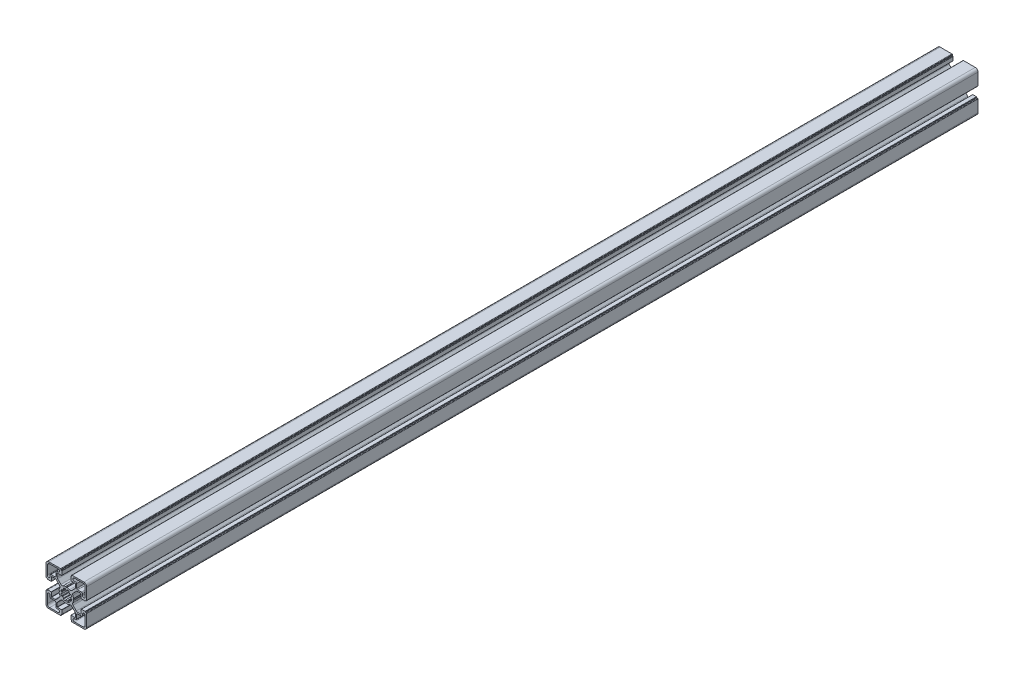
SolidWorks part; units mm, degrees
ref_plane "Front Plane" through (0, 0, 0) normal (0, 0, 1) x (1, 0, 0)
ref_plane "Top Plane" through (0, 0, 0) normal (0, 1, 0) x (1, 0, 0)
ref_plane "Right Plane" through (0, 0, 0) normal (1, 0, 0) x (0, 0, -1)
sketch "Sketch1" plane through (0, 0, 0) normal (0, 0, 1) x (1, 0, 0)
  line L0 (10.55, 18) -> (9, 18)
  line L1 (18.5, 21) -> (9, 21)
  line L2 (21, 9.0002) -> (21, 18.5)
  line L3 (18, 9.0002) -> (18, 10.55)
  line L4 (17, 11.55) -> (12.55, 11.55)
  line L5 (11.55, 12.55) -> (11.55, 17)
  line L6 (7.974, 0.7926) -> (7.5401, 0.0468)
  line L7 (-0.8674, 4.9242) -> (-0.9675, 5.4811)
  line L8 (-3.1913, 4.5626) -> (-2.864, 4.0985)
  line L9 (-4.0897, 2.8765) -> (-4.5668, 3.2082)
  line L10 (-5.4897, 0.9862) -> (-4.9205, 0.8878)
  line L11 (11.1298, 9.425) -> (7.5635, 5.8587)
  line L12 (16.3169, 9.9945) -> (12.5048, 9.9945)
  line L13 (16.5169, 5.2) -> (16.5169, 9.7945)
  line L14 (20.7196, 5) -> (16.7169, 5)
  line L15 (21.0196, 5.3) -> (21.0196, 5.5)
  line L16 (22, 5.8) -> (21.3196, 5.8)
  line L17 (22.5, 6.3) -> (22.5, 19.5)
  line L18 (19.5, 22.5) -> (6.3757, 22.5)
  line L19 (5.8757, 21.3) -> (5.8757, 22)
  line L20 (5.5757, 21) -> (5.3, 21)
  line L21 (5, 16.6668) -> (5, 20.7)
  line L22 (9.9054, 16.4668) -> (5.2, 16.4668)
  line L23 (10.1054, 12.4716) -> (10.1054, 16.2668)
  line L24 (5.9449, 7.4827) -> (9.5196, 11.0574)
  line L25 (0.1126, 7.6069) -> (0.7547, 7.9748)
  line L26 (5.4897, 0.9862) -> (4.9205, 0.8878)
  line L27 (4.0897, 2.8765) -> (4.5668, 3.2082)
  line L28 (3.1913, 4.5626) -> (2.864, 4.0985)
  line L29 (0.8674, 4.9242) -> (0.9675, 5.4811)
  line L30 (-10.55, -18) -> (-9, -18)
  line L31 (-18.5, -21) -> (-9, -21)
  line L32 (-21, -9.0002) -> (-21, -18.5)
  line L33 (-18, -9.0002) -> (-18, -10.55)
  line L34 (-17, -11.55) -> (-12.55, -11.55)
  line L35 (-11.55, -12.55) -> (-11.55, -17)
  line L36 (-7.974, -0.7926) -> (-7.5401, -0.0468)
  line L37 (-11.1298, -9.425) -> (-7.5635, -5.8587)
  line L38 (-16.3169, -9.9945) -> (-12.5048, -9.9945)
  line L39 (-16.5169, -5.2) -> (-16.5169, -9.7945)
  line L40 (-20.7196, -5) -> (-16.7169, -5)
  line L41 (-21.0196, -5.3) -> (-21.0196, -5.5)
  line L42 (-22, -5.8) -> (-21.3196, -5.8)
  line L43 (-22.5, -6.3) -> (-22.5, -19.5)
  line L44 (-19.5, -22.5) -> (-6.3757, -22.5)
  line L45 (-5.8757, -21.3) -> (-5.8757, -22)
  line L46 (-5.5757, -21) -> (-5.3, -21)
  line L47 (-5, -16.6668) -> (-5, -20.7)
  line L48 (-9.9054, -16.4668) -> (-5.2, -16.4668)
  line L49 (-10.1054, -12.4716) -> (-10.1054, -16.2668)
  line L50 (-5.9449, -7.4827) -> (-9.5196, -11.0574)
  line L51 (-0.1126, -7.6069) -> (-0.7547, -7.9748)
  line L52 (0.8674, -4.9242) -> (0.9675, -5.4811)
  line L53 (3.1913, -4.5626) -> (2.864, -4.0985)
  line L54 (4.0897, -2.8765) -> (4.5668, -3.2082)
  line L55 (5.4897, -0.9862) -> (4.9205, -0.8878)
  line L56 (0.1126, -7.6069) -> (0.7547, -7.9748)
  line L57 (5.9449, -7.4827) -> (9.5196, -11.0574)
  line L58 (10.1054, -12.4716) -> (10.1054, -16.2668)
  line L59 (9.9054, -16.4668) -> (5.2, -16.4668)
  line L60 (5, -16.6668) -> (5, -20.7)
  line L61 (5.5757, -21) -> (5.3, -21)
  line L62 (-0.1126, 7.6069) -> (-0.7547, 7.9748)
  line L63 (-5.9449, 7.4827) -> (-9.5196, 11.0574)
  line L64 (-10.1054, 12.4716) -> (-10.1054, 16.2668)
  line L65 (-9.9054, 16.4668) -> (-5.2, 16.4668)
  line L66 (-5, 16.6668) -> (-5, 20.7)
  line L67 (-5.5757, 21) -> (-5.3, 21)
  line L68 (-5.8757, 21.3) -> (-5.8757, 22)
  line L69 (-19.5, 22.5) -> (-6.3757, 22.5)
  line L70 (-22.5, 6.3) -> (-22.5, 19.5)
  line L71 (-22, 5.8) -> (-21.3196, 5.8)
  line L72 (-21.0196, 5.3) -> (-21.0196, 5.5)
  line L73 (-20.7196, 5) -> (-16.7169, 5)
  line L74 (-16.5169, 5.2) -> (-16.5169, 9.7945)
  line L75 (-16.3169, 9.9945) -> (-12.5048, 9.9945)
  line L76 (-11.1298, 9.425) -> (-7.5635, 5.8587)
  line L77 (-7.974, 0.7926) -> (-7.5401, 0.0468)
  line L78 (5.8757, -21.3) -> (5.8757, -22)
  line L79 (19.5, -22.5) -> (6.3757, -22.5)
  line L80 (22.5, -6.3) -> (22.5, -19.5)
  line L81 (22, -5.8) -> (21.3196, -5.8)
  line L82 (21.0196, -5.3) -> (21.0196, -5.5)
  line L83 (20.7196, -5) -> (16.7169, -5)
  line L84 (16.5169, -5.2) -> (16.5169, -9.7945)
  line L85 (16.3169, -9.9945) -> (12.5048, -9.9945)
  line L86 (11.1298, -9.425) -> (7.5635, -5.8587)
  line L87 (-5.4897, -0.9862) -> (-4.9205, -0.8878)
  line L88 (-4.0897, -2.8765) -> (-4.5668, -3.2082)
  line L89 (-3.1913, -4.5626) -> (-2.864, -4.0985)
  line L90 (-0.8674, -4.9242) -> (-0.9675, -5.4811)
  line L91 (7.974, -0.7926) -> (7.5401, -0.0468)
  line L92 (-11.55, 12.55) -> (-11.55, 17)
  line L93 (-17, 11.55) -> (-12.55, 11.55)
  line L94 (-18, 9.0002) -> (-18, 10.55)
  line L95 (-21, 9.0002) -> (-21, 18.5)
  line L96 (-18.5, 21) -> (-9, 21)
  line L97 (-10.55, 18) -> (-9, 18)
  line L98 (11.55, -12.55) -> (11.55, -17)
  line L99 (17, -11.55) -> (12.55, -11.55)
  line L100 (18, -9.0002) -> (18, -10.55)
  line L101 (21, -9.0002) -> (21, -18.5)
  line L102 (18.5, -21) -> (9, -21)
  line L103 (10.55, -18) -> (9, -18)
  line L104 (-33.3633, 0) -> (37.7265, 0) construction
  line L105 (0, 32.2957) -> (0, -36.0465) construction
  arc A0 (9, 18) -> (9, 21) centre (9, 19.5) cw
  arc A1 (18.5, 21) -> (21, 18.5) centre (18.5, 18.5) cw
  arc A2 (21, 9.0002) -> (18, 9.0002) centre (19.5, 9.0002) cw
  arc A3 (17, 11.55) -> (18, 10.55) centre (17, 10.55) cw
  arc A4 (12.55, 11.55) -> (11.55, 12.55) centre (12.55, 12.55) cw
  arc A5 (10.55, 18) -> (11.55, 17) centre (10.55, 17) cw
  arc A6 (7.5313, 0) -> (7.5401, 0.0468) centre (7.7309, -0.013) cw
  arc A7 (8, 0.9141) -> (7.974, 0.7926) centre (7.8011, 0.8932) cw
  arc A8 (7.2004, 3.6119) -> (8, 0.9141) centre (0.0496, 0.0249) cw
  arc A9 (7.2004, 3.6119) -> (7.5635, 5.8587) centre (8.9385, 4.4837) cw
  arc A10 (11.1298, 9.425) -> (12.5048, 9.9945) centre (12.5048, 8.05) cw
  arc A11 (16.3169, 9.9945) -> (16.5169, 9.7945) centre (16.3169, 9.7945) cw
  arc A12 (16.7169, 5) -> (16.5169, 5.2) centre (16.7169, 5.2) cw
  arc A13 (21.0196, 5.3) -> (20.7196, 5) centre (20.7196, 5.3) cw
  arc A14 (0.8674, 4.9242) -> (-0.8674, 4.9242) centre (0, 0) ccw
  arc A15 (-0.9675, 5.4811) -> (-1.5951, 5.8941) centre (-1.4627, 5.4119) ccw
  arc A16 (-1.5951, 5.8941) -> (-3.0444, 5.2994) centre (-0.0235, 0) ccw
  arc A17 (-3.0444, 5.2994) -> (-3.1913, 4.5626) centre (-2.7943, 4.8665) ccw
  arc A18 (-2.864, 4.0985) -> (-4.0897, 2.8765) centre (0, 0) ccw
  arc A19 (-4.5668, 3.2082) -> (-5.3025, 3.0565) centre (-4.868, 2.8091) ccw
  arc A20 (-5.3025, 3.0565) -> (-5.9068, 1.6112) centre (-0.0235, 0) ccw
  arc A21 (-5.9068, 1.6112) -> (-5.4897, 0.9862) centre (-5.4239, 1.4819) ccw
  arc A22 (-4.9205, 0.8878) -> (-5, 0) centre (0, 0) ccw
  arc A23 (21.0196, 5.5) -> (21.3196, 5.8) centre (21.3196, 5.5) cw
  arc A24 (22.5, 6.3) -> (22, 5.8) centre (22, 6.3) cw
  arc A25 (19.5, 22.5) -> (22.5, 19.5) centre (19.5, 19.5) cw
  arc A26 (5.8757, 22) -> (6.3757, 22.5) centre (6.3757, 22) cw
  arc A27 (5.8757, 21.3) -> (5.5757, 21) centre (5.5757, 21.3) cw
  arc A28 (5, 20.7) -> (5.3, 21) centre (5.3, 20.7) cw
  arc A29 (5.2, 16.4668) -> (5, 16.6668) centre (5.2, 16.6668) cw
  arc A30 (9.9054, 16.4668) -> (10.1054, 16.2668) centre (9.9054, 16.2668) cw
  arc A31 (10.1054, 12.4716) -> (9.5196, 11.0574) centre (8.1054, 12.4716) cw
  arc A32 (5.9449, 7.4827) -> (3.6665, 7.1733) centre (4.5855, 8.9496) cw
  arc A33 (0.8764, 8) -> (3.6665, 7.1733) centre (0.0235, 0) cw
  arc A34 (0.7547, 7.9748) -> (0.8764, 8) centre (0.8542, 7.8013) cw
  arc A35 (0.1126, 7.6069) -> (0, 7.531) centre (-0.0489, 7.7249) cw
  arc A36 (4.9205, 0.8878) -> (5, 0) centre (0, 0) cw
  arc A37 (5.9068, 1.6112) -> (5.4897, 0.9862) centre (5.4239, 1.4819) cw
  arc A38 (5.3025, 3.0565) -> (5.9068, 1.6112) centre (0.0235, 0) cw
  arc A39 (4.5668, 3.2082) -> (5.3025, 3.0565) centre (4.868, 2.8091) cw
  arc A40 (2.864, 4.0985) -> (4.0897, 2.8765) centre (0, 0) cw
  arc A41 (3.0444, 5.2994) -> (3.1913, 4.5626) centre (2.7943, 4.8665) cw
  arc A42 (1.5951, 5.8941) -> (3.0444, 5.2994) centre (0.0235, 0) cw
  arc A43 (0.9675, 5.4811) -> (1.5951, 5.8941) centre (1.4627, 5.4119) cw
  arc A44 (-9, -18) -> (-9, -21) centre (-9, -19.5) cw
  arc A45 (-18.5, -21) -> (-21, -18.5) centre (-18.5, -18.5) cw
  arc A46 (-21, -9.0002) -> (-18, -9.0002) centre (-19.5, -9.0002) cw
  arc A47 (-17, -11.55) -> (-18, -10.55) centre (-17, -10.55) cw
  arc A48 (-12.55, -11.55) -> (-11.55, -12.55) centre (-12.55, -12.55) cw
  arc A49 (-10.55, -18) -> (-11.55, -17) centre (-10.55, -17) cw
  arc A50 (-7.5313, 0) -> (-7.5401, -0.0468) centre (-7.7309, 0.013) cw
  arc A51 (-8, -0.9141) -> (-7.974, -0.7926) centre (-7.8011, -0.8932) cw
  arc A52 (-7.2004, -3.6119) -> (-8, -0.9141) centre (-0.0496, -0.0249) cw
  arc A53 (-7.2004, -3.6119) -> (-7.5635, -5.8587) centre (-8.9385, -4.4837) cw
  arc A54 (-11.1298, -9.425) -> (-12.5048, -9.9945) centre (-12.5048, -8.05) cw
  arc A55 (-16.3169, -9.9945) -> (-16.5169, -9.7945) centre (-16.3169, -9.7945) cw
  arc A56 (-16.7169, -5) -> (-16.5169, -5.2) centre (-16.7169, -5.2) cw
  arc A57 (-21.0196, -5.3) -> (-20.7196, -5) centre (-20.7196, -5.3) cw
  arc A58 (-21.0196, -5.5) -> (-21.3196, -5.8) centre (-21.3196, -5.5) cw
  arc A59 (-22.5, -6.3) -> (-22, -5.8) centre (-22, -6.3) cw
  arc A60 (-19.5, -22.5) -> (-22.5, -19.5) centre (-19.5, -19.5) cw
  arc A61 (-5.8757, -22) -> (-6.3757, -22.5) centre (-6.3757, -22) cw
  arc A62 (-5.8757, -21.3) -> (-5.5757, -21) centre (-5.5757, -21.3) cw
  arc A63 (-5, -20.7) -> (-5.3, -21) centre (-5.3, -20.7) cw
  arc A64 (-5.2, -16.4668) -> (-5, -16.6668) centre (-5.2, -16.6668) cw
  arc A65 (-9.9054, -16.4668) -> (-10.1054, -16.2668) centre (-9.9054, -16.2668) cw
  arc A66 (-10.1054, -12.4716) -> (-9.5196, -11.0574) centre (-8.1054, -12.4716) cw
  arc A67 (-5.9449, -7.4827) -> (-3.6665, -7.1733) centre (-4.5855, -8.9496) cw
  arc A68 (-0.8764, -8) -> (-3.6665, -7.1733) centre (-0.0235, 0) cw
  arc A69 (-0.7547, -7.9748) -> (-0.8764, -8) centre (-0.8542, -7.8013) cw
  arc A70 (-0.1126, -7.6069) -> (0, -7.531) centre (0.0489, -7.7249) cw
  arc A71 (0.9675, -5.4811) -> (1.5951, -5.8941) centre (1.4627, -5.4119) ccw
  arc A72 (1.5951, -5.8941) -> (3.0444, -5.2994) centre (0.0235, 0) ccw
  arc A73 (3.0444, -5.2994) -> (3.1913, -4.5626) centre (2.7943, -4.8665) ccw
  arc A74 (2.864, -4.0985) -> (4.0897, -2.8765) centre (0, 0) ccw
  arc A75 (4.5668, -3.2082) -> (5.3025, -3.0565) centre (4.868, -2.8091) ccw
  arc A76 (5.3025, -3.0565) -> (5.9068, -1.6112) centre (0.0235, 0) ccw
  arc A77 (5.9068, -1.6112) -> (5.4897, -0.9862) centre (5.4239, -1.4819) ccw
  arc A78 (4.9205, -0.8878) -> (5, 0) centre (0, 0) ccw
  arc A79 (0.1126, -7.6069) -> (0, -7.531) centre (-0.0489, -7.7249) ccw
  arc A80 (0.7547, -7.9748) -> (0.8764, -8) centre (0.8542, -7.8013) ccw
  arc A81 (0.8764, -8) -> (3.6665, -7.1733) centre (0.0235, 0) ccw
  arc A82 (5.9449, -7.4827) -> (3.6665, -7.1733) centre (4.5855, -8.9496) ccw
  arc A83 (10.1054, -12.4716) -> (9.5196, -11.0574) centre (8.1054, -12.4716) ccw
  arc A84 (9.9054, -16.4668) -> (10.1054, -16.2668) centre (9.9054, -16.2668) ccw
  arc A85 (5.2, -16.4668) -> (5, -16.6668) centre (5.2, -16.6668) ccw
  arc A86 (5, -20.7) -> (5.3, -21) centre (5.3, -20.7) ccw
  arc A87 (5.8757, -21.3) -> (5.5757, -21) centre (5.5757, -21.3) ccw
  arc A88 (-0.1126, 7.6069) -> (0, 7.531) centre (0.0489, 7.7249) ccw
  arc A89 (-0.7547, 7.9748) -> (-0.8764, 8) centre (-0.8542, 7.8013) ccw
  arc A90 (-0.8764, 8) -> (-3.6665, 7.1733) centre (-0.0235, 0) ccw
  arc A91 (-5.9449, 7.4827) -> (-3.6665, 7.1733) centre (-4.5855, 8.9496) ccw
  arc A92 (-10.1054, 12.4716) -> (-9.5196, 11.0574) centre (-8.1054, 12.4716) ccw
  arc A93 (-9.9054, 16.4668) -> (-10.1054, 16.2668) centre (-9.9054, 16.2668) ccw
  arc A94 (-5.2, 16.4668) -> (-5, 16.6668) centre (-5.2, 16.6668) ccw
  arc A95 (-5, 20.7) -> (-5.3, 21) centre (-5.3, 20.7) ccw
  arc A96 (-5.8757, 21.3) -> (-5.5757, 21) centre (-5.5757, 21.3) ccw
  arc A97 (-5.8757, 22) -> (-6.3757, 22.5) centre (-6.3757, 22) ccw
  arc A98 (-19.5, 22.5) -> (-22.5, 19.5) centre (-19.5, 19.5) ccw
  arc A99 (-22.5, 6.3) -> (-22, 5.8) centre (-22, 6.3) ccw
  arc A100 (-21.0196, 5.5) -> (-21.3196, 5.8) centre (-21.3196, 5.5) ccw
  arc A101 (-21.0196, 5.3) -> (-20.7196, 5) centre (-20.7196, 5.3) ccw
  arc A102 (-16.7169, 5) -> (-16.5169, 5.2) centre (-16.7169, 5.2) ccw
  arc A103 (-16.3169, 9.9945) -> (-16.5169, 9.7945) centre (-16.3169, 9.7945) ccw
  arc A104 (-11.1298, 9.425) -> (-12.5048, 9.9945) centre (-12.5048, 8.05) ccw
  arc A105 (-7.2004, 3.6119) -> (-7.5635, 5.8587) centre (-8.9385, 4.4837) ccw
  arc A106 (-7.2004, 3.6119) -> (-8, 0.9141) centre (-0.0496, 0.0249) ccw
  arc A107 (-8, 0.9141) -> (-7.974, 0.7926) centre (-7.8011, 0.8932) ccw
  arc A108 (-7.5313, 0) -> (-7.5401, 0.0468) centre (-7.7309, -0.013) ccw
  arc A109 (5.8757, -22) -> (6.3757, -22.5) centre (6.3757, -22) ccw
  arc A110 (19.5, -22.5) -> (22.5, -19.5) centre (19.5, -19.5) ccw
  arc A111 (22.5, -6.3) -> (22, -5.8) centre (22, -6.3) ccw
  arc A112 (21.0196, -5.5) -> (21.3196, -5.8) centre (21.3196, -5.5) ccw
  arc A113 (-4.9205, -0.8878) -> (-5, 0) centre (0, 0) cw
  arc A114 (-5.9068, -1.6112) -> (-5.4897, -0.9862) centre (-5.4239, -1.4819) cw
  arc A115 (-5.3025, -3.0565) -> (-5.9068, -1.6112) centre (-0.0235, 0) cw
  arc A116 (-4.5668, -3.2082) -> (-5.3025, -3.0565) centre (-4.868, -2.8091) cw
  arc A117 (-2.864, -4.0985) -> (-4.0897, -2.8765) centre (0, 0) cw
  arc A118 (-3.0444, -5.2994) -> (-3.1913, -4.5626) centre (-2.7943, -4.8665) cw
  arc A119 (-1.5951, -5.8941) -> (-3.0444, -5.2994) centre (-0.0235, 0) cw
  arc A120 (-0.9675, -5.4811) -> (-1.5951, -5.8941) centre (-1.4627, -5.4119) cw
  arc A121 (0.8674, -4.9242) -> (-0.8674, -4.9242) centre (0, 0) cw
  arc A122 (21.0196, -5.3) -> (20.7196, -5) centre (20.7196, -5.3) ccw
  arc A123 (16.7169, -5) -> (16.5169, -5.2) centre (16.7169, -5.2) ccw
  arc A124 (-10.55, 18) -> (-11.55, 17) centre (-10.55, 17) ccw
  arc A125 (-12.55, 11.55) -> (-11.55, 12.55) centre (-12.55, 12.55) ccw
  arc A126 (-17, 11.55) -> (-18, 10.55) centre (-17, 10.55) ccw
  arc A127 (-21, 9.0002) -> (-18, 9.0002) centre (-19.5, 9.0002) ccw
  arc A128 (-18.5, 21) -> (-21, 18.5) centre (-18.5, 18.5) ccw
  arc A129 (-9, 18) -> (-9, 21) centre (-9, 19.5) ccw
  arc A130 (16.3169, -9.9945) -> (16.5169, -9.7945) centre (16.3169, -9.7945) ccw
  arc A131 (11.1298, -9.425) -> (12.5048, -9.9945) centre (12.5048, -8.05) ccw
  arc A132 (7.2004, -3.6119) -> (7.5635, -5.8587) centre (8.9385, -4.4837) ccw
  arc A133 (7.2004, -3.6119) -> (8, -0.9141) centre (0.0496, -0.0249) ccw
  arc A134 (8, -0.9141) -> (7.974, -0.7926) centre (7.8011, -0.8932) ccw
  arc A135 (7.5313, 0) -> (7.5401, -0.0468) centre (7.7309, 0.013) ccw
  arc A136 (10.55, -18) -> (11.55, -17) centre (10.55, -17) ccw
  arc A137 (12.55, -11.55) -> (11.55, -12.55) centre (12.55, -12.55) ccw
  arc A138 (17, -11.55) -> (18, -10.55) centre (17, -10.55) ccw
  arc A139 (21, -9.0002) -> (18, -9.0002) centre (19.5, -9.0002) ccw
  arc A140 (18.5, -21) -> (21, -18.5) centre (18.5, -18.5) ccw
  arc A141 (9, -18) -> (9, -21) centre (9, -19.5) ccw
  dimension "D6" = 12.2
  dimension "D8" = 10
  dimension "D1" = 10
  dimension "D2" = 45
  dimension "D3" = 45
  dimension "D4" = 10
  dimension "D5" = 14.5
  dimension "D7" = 22.5
extrude "Base-Extrude" add sketch "Sketch1" against normal blind 988
